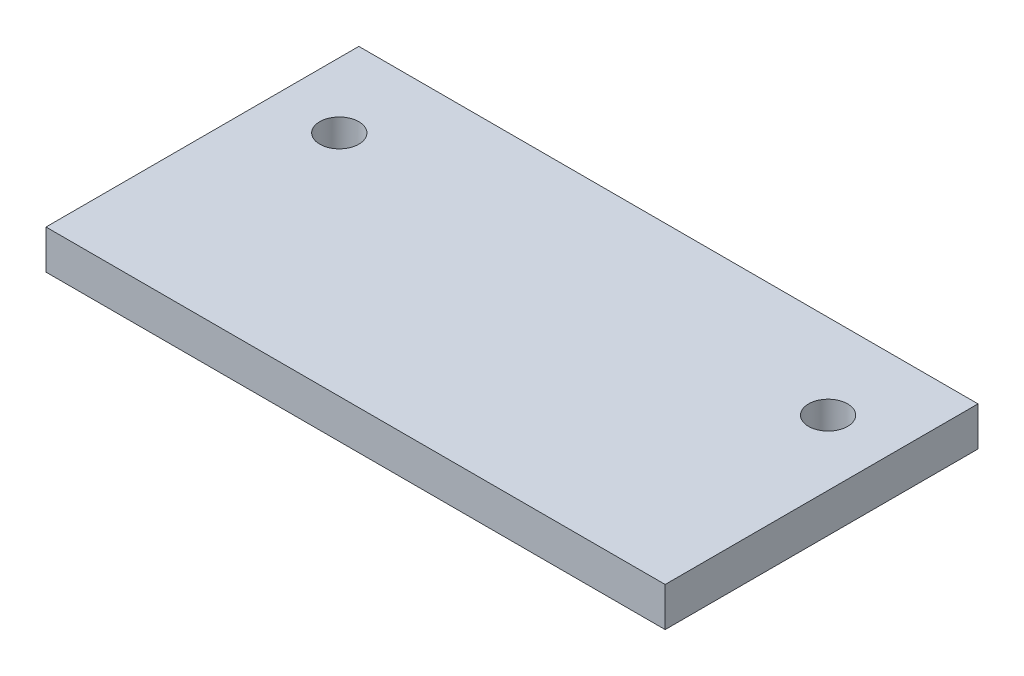
SolidWorks part; units mm, degrees
ref_plane "Front Plane" through (0, 0, 0) normal (0, 0, 1) x (1, 0, 0)
ref_plane "Top Plane" through (0, 0, 0) normal (0, 1, 0) x (1, 0, 0)
ref_plane "Right Plane" through (0, 0, 0) normal (1, 0, 0) x (0, 0, -1)
sketch "Sketch2" plane through (0, 0, 0) normal (0, 1, 0) x (1, 0, 0)
  line L1 (0, 0) -> (47.5, 0)
  line L2 (0, 0) -> (0, 35)
  line L3 (0, 35) -> (47.5, 35)
  line L4 (47.5, 0) -> (47.5, 35)
  dimension "D1" = 47.5
  dimension "D2" = 35
extrude "Boss-Extrude1" add sketch "Sketch2" along normal blind 3
hole_wizard "Ø3.0mm Dowel Hole1" positions "Sketch3" profile "Sketch4" hole size "Ø3.0" standard "ANSI Metric" end condition up to next
sketch "Sketch3" plane through (0, 3, 0) normal (0, 1, 0) x (1, 0, 0)
  line L0 (0, 17.5) -> (47.5, 17.5) construction
  line L1 (0, 35) -> (0, 0) construction
  line L2 (47.5, 0) -> (47.5, 35) construction
  line L4 (47.5, 35) -> (0, 35) construction
  point P0 (5, 17.5)
  point P2 (42.5, 17.5)
  dimension "D1" = 17.5
  dimension "D2" = 5
  dimension "D3" = 5
sketch "Sketch4" plane through (5, 3, -17.5) normal (1, 0, 0) x (0, 0, 1)
  line L0 (0, 0) -> (0, 3)
  line L1 (0, 3) -> (1.5, 3)
  line L2 (1.5, 3) -> (1.5, 0)
  line L5 (1.5, 0) -> (0, 0)
  line L11 (0, -6.35) -> (0, 107.95) construction
  dimension "Thru Hole Dia." = 3
  dimension "Thru Hole Depth" = 3
sketch "Sketch5" plane through (0, 3, 0) normal (0, 1, 0) x (1, 0, 0)
  line L0 (47.5, 0) -> (47.5, 35) construction
  line L1 (0, 35) -> (47.5, 35)
  line L2 (0, 35) -> (0, 24)
  line L3 (0, 24) -> (47.5, 24)
  line L4 (47.5, 35) -> (47.5, 24)
  dimension "D1" = 11
extrude "Cut-Extrude1" cut sketch "Sketch5" against normal up to next
